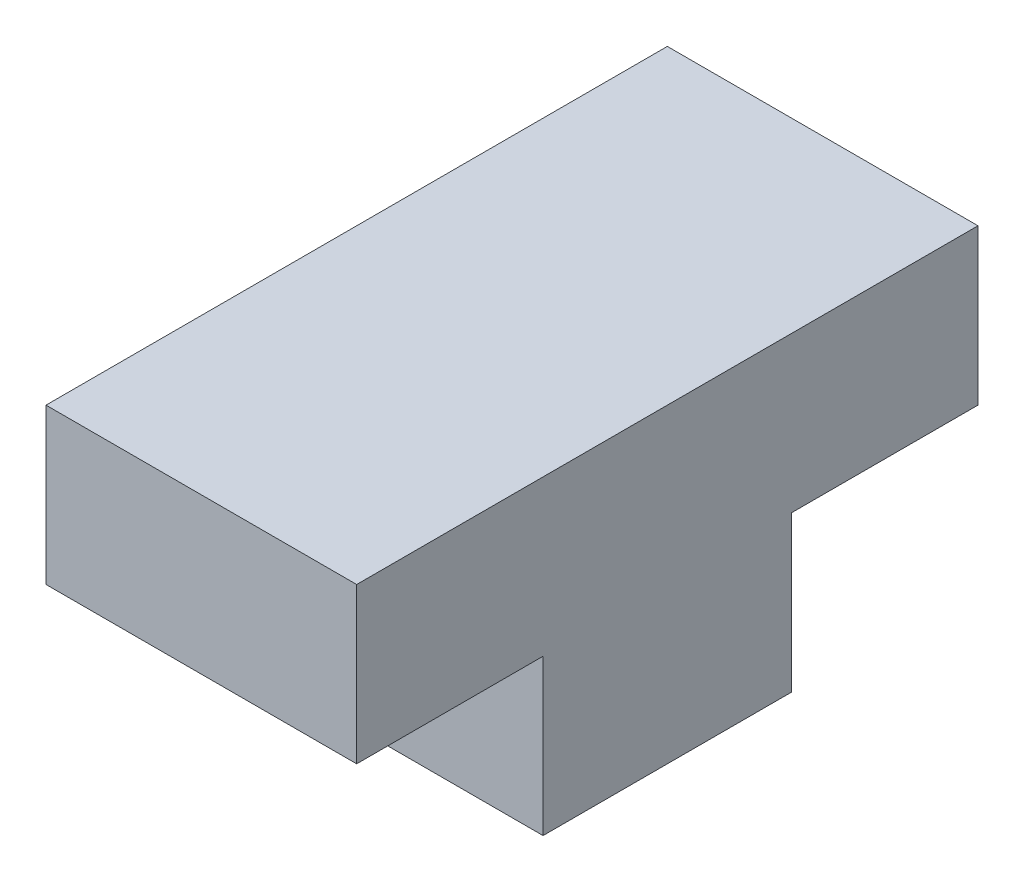
SolidWorks part; units mm, degrees
ref_plane "Front Plane" through (0, 0, 0) normal (0, 0, 1) x (1, 0, 0)
ref_plane "Top Plane" through (0, 0, 0) normal (0, 1, 0) x (1, 0, 0)
ref_plane "Right Plane" through (0, 0, 0) normal (1, 0, 0) x (0, 0, -1)
sketch "Sketch1" plane through (0, 0, 0) normal (1, 0, 0) x (0, 0, -1)
  line L0 (-4, 0) -> (4, 0)
  line L1 (4, 0) -> (4, 5)
  line L2 (4, 5) -> (10, 5)
  line L3 (10, 5) -> (10, 10)
  line L4 (10, 10) -> (-10, 10)
  line L5 (0, 55) -> (0, -55) construction
  line L6 (-10, 5) -> (-10, 10)
  line L7 (-4, 5) -> (-10, 5)
  line L8 (-4, 0) -> (-4, 5)
  point P7 (0, 0)
  point P11 (0, 10)
  point P14 (0, 0)
  dimension "D1" = 4
  dimension "D2" = 5
  dimension "D3" = 5
  dimension "D4" = 10
extrude "Boss-Extrude1" add sketch "Sketch1" along normal blind 10
